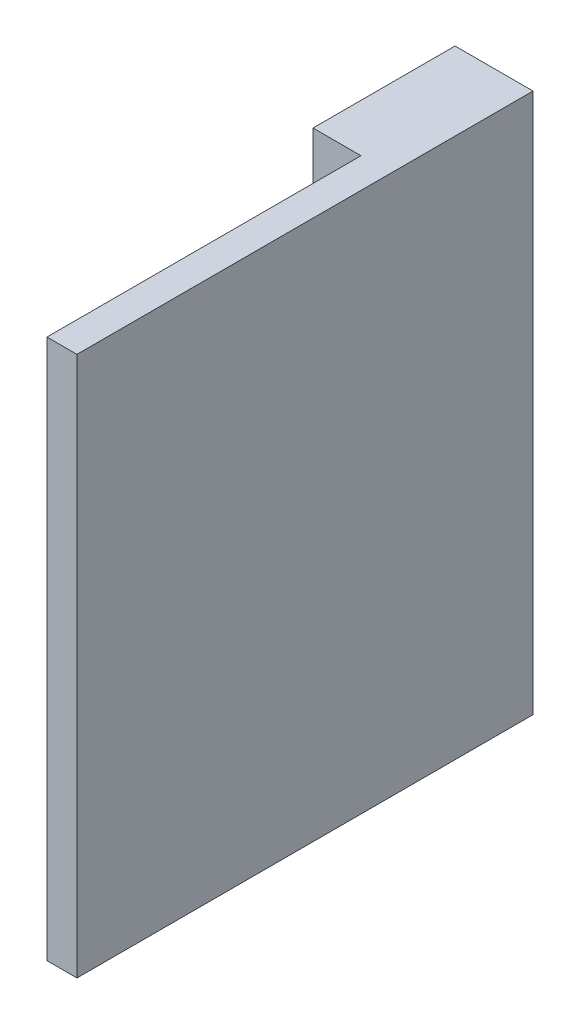
SolidWorks part; units mm, degrees
ref_plane "Plano frontal" through (0, 0, 0) normal (0, 0, 1) x (1, 0, 0)
ref_plane "Plano superior" through (0, 0, 0) normal (0, 1, 0) x (1, 0, 0)
ref_plane "Plano direito" through (0, 0, 0) normal (1, 0, 0) x (0, 0, -1)
sketch "Esboço1" plane through (0, 0, 0) normal (0, 1, 0) x (1, 0, 0)
  line L0 (0, 0) -> (150, 0)
  line L1 (150, 0) -> (150, 2280)
  line L2 (150, 2280) -> (-240, 2280)
  line L3 (-240, 2280) -> (-240, 1570)
  line L4 (-240, 1570) -> (0, 1570)
  line L5 (0, 1570) -> (0, 0)
  dimension "D1" = 150
  dimension "D2" = 710
  dimension "D3" = 240
  dimension "D4" = 2280
extrude "Ressalto-extrusão1" add sketch "Esboço1" along normal blind 2700
